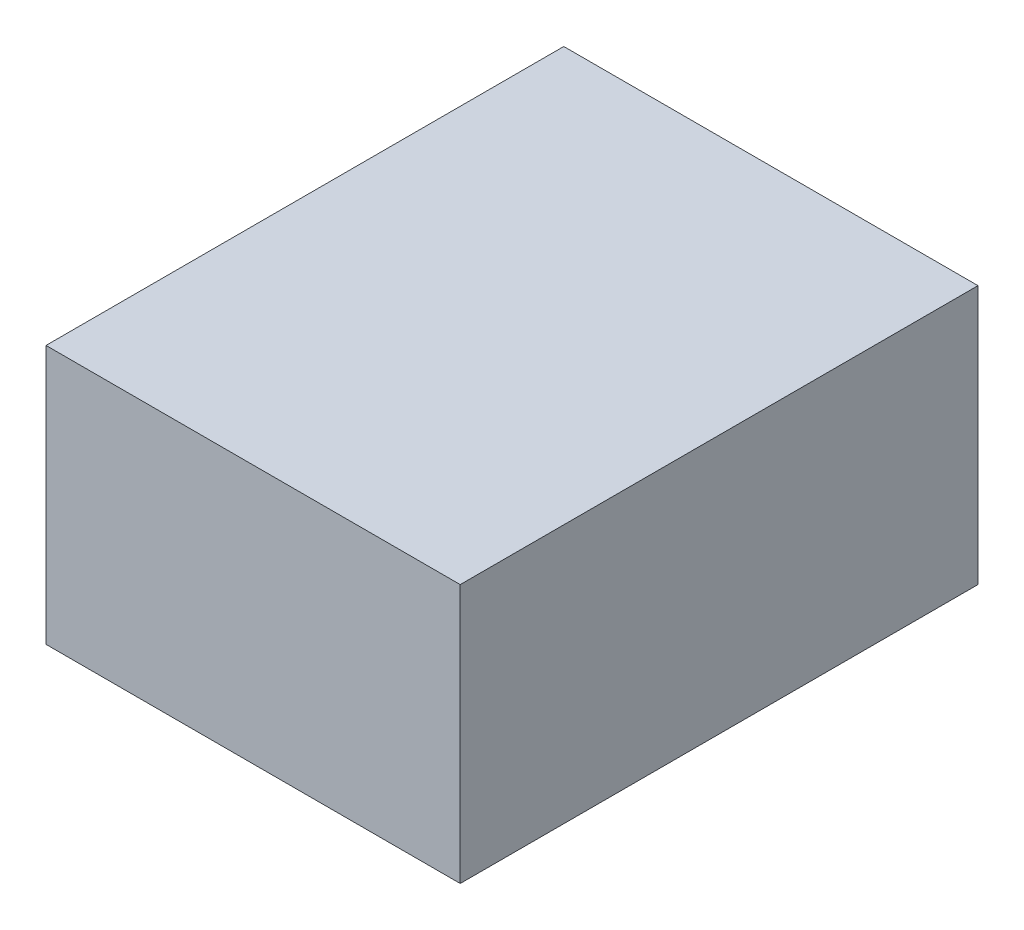
SolidWorks part; units mm, degrees
ref_plane "Front Plane" through (0, 0, 0) normal (0, 0, 1) x (1, 0, 0)
ref_plane "Top Plane" through (0, 0, 0) normal (0, 1, 0) x (1, 0, 0)
ref_plane "Right Plane" through (0, 0, 0) normal (1, 0, 0) x (0, 0, -1)
sketch "Sketch1" plane through (0, 0, 0) normal (0, 1, 0) x (1, 0, 0)
  line L1 (-20, -25) -> (20, -25)
  line L2 (-20, -25) -> (-20, 25)
  line L3 (-20, 25) -> (20, 25)
  line L4 (20, -25) -> (20, 25)
  line L5 (-20, -25) -> (20, 25) construction
  line L6 (-20, 25) -> (20, -25) construction
  point P0 (0, 0)
  dimension "D1" = 50
  dimension "D2" = 40
extrude "Boss-Extrude1" add sketch "Sketch1" along normal blind 25 from offset 3
